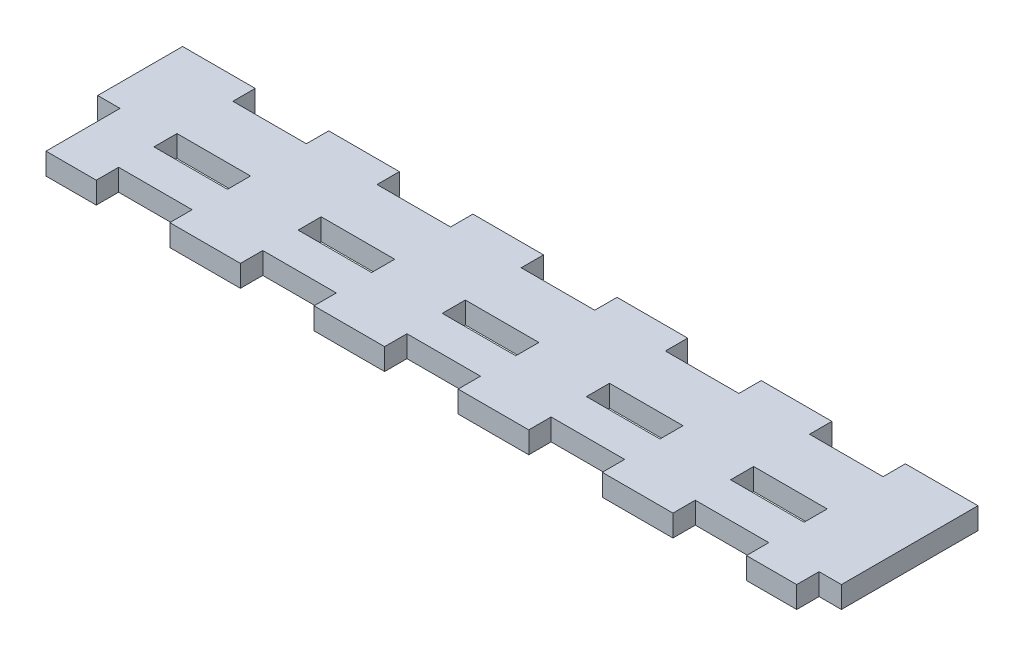
SolidWorks part; units mm, degrees
ref_plane "Front Plane" through (0, 0, 0) normal (0, 0, 1) x (1, 0, 0)
ref_plane "Top Plane" through (0, 0, 0) normal (0, 1, 0) x (1, 0, 0)
ref_plane "Right Plane" through (0, 0, 0) normal (1, 0, 0) x (0, 0, -1)
sketch "Sketch1" plane through (0, 0, 0) normal (0, 1, 0) x (1, 0, 0)
  line L0 (0, 0) -> (0, 21) construction
  line L2 (-55.1722, -44.793) -> (55.1722, -44.793)
  line L3 (-55.1722, -44.793) -> (-55.1722, -66.843)
  line L4 (-55.1722, -66.843) -> (55.1722, -66.843)
  line L5 (55.1722, -44.793) -> (55.1722, -66.843)
  circle A0 centre (0, 0) radius 21 construction
  circle A1 centre (0, 0) radius 21 construction
extrude "Boss-Extrude1" add sketch "Sketch1" against normal up to vertex (3 mm away)
sketch "Sketch2" plane through (0, 0, 0) normal (0, 1, 0) x (1, 0, 0)
  line L1 (-45, -55.743) -> (-35, -55.743)
  line L2 (45, -63.843) -> (45, -66.843)
  line L3 (-55.1722, -56.6708) -> (-52.1722, -56.6708) construction
  line L4 (55.1722, -44.793) -> (-55.1722, -44.793)
  line L5 (55.1722, -66.843) -> (55.1722, -44.793)
  line L6 (-55.1722, -66.843) -> (55.1722, -66.843)
  line L7 (-55.1722, -44.793) -> (-55.1722, -66.843)
  line L8 (55.1722, -44.793) -> (-55.1722, -44.793) construction
  line L9 (55.1722, -66.843) -> (55.1722, -44.793) construction
  line L10 (-55.1722, -66.843) -> (55.1722, -66.843) construction
  line L11 (-55.1722, -44.793) -> (-55.1722, -66.843) construction
  line L12 (-52.1722, -56.6708) -> (-52.1722, -66.843) construction
  line L14 (-45, -44.793) -> (-45, -47.793)
  line L15 (-45, -66.843) -> (-35, -66.843)
  line L16 (-35, -44.793) -> (-35, -47.793)
  line L17 (35, -63.843) -> (35, -66.843)
  line L18 (-25, -44.793) -> (-25, -47.793)
  line L19 (25, -63.843) -> (25, -66.843)
  line L20 (-15, -44.793) -> (-15, -47.793)
  line L21 (15, -63.843) -> (15, -66.843)
  line L22 (-5, -44.793) -> (-5, -47.793)
  line L23 (5, -63.843) -> (5, -66.843)
  line L24 (5, -44.793) -> (5, -47.793)
  line L25 (-5, -63.843) -> (-5, -66.843)
  line L26 (15, -44.793) -> (15, -47.793)
  line L27 (-15, -63.843) -> (-15, -66.843)
  line L28 (25, -44.793) -> (25, -47.793)
  line L29 (-25, -63.843) -> (-25, -66.843)
  line L30 (35, -44.793) -> (35, -47.793)
  line L31 (-35, -63.843) -> (-35, -66.843)
  line L32 (45, -44.793) -> (45, -47.793)
  line L33 (52.1722, -63.843) -> (55.1722, -63.843)
  line L34 (52.1722, -63.843) -> (52.1722, -66.843)
  line L37 (-45, -58.743) -> (-35, -58.743)
  line L38 (-45, -63.843) -> (-35, -63.843)
  line L39 (-45, -63.843) -> (-45, -66.843)
  line L40 (-45, -47.793) -> (-35, -47.793)
  line L41 (-45, -55.743) -> (-45, -58.743)
  line L42 (-35, -55.743) -> (-35, -58.743)
  line L43 (-25, -55.743) -> (-25, -58.743)
  line L44 (-15, -55.743) -> (-15, -58.743)
  line L45 (-5, -55.743) -> (-5, -58.743)
  line L46 (5, -55.743) -> (5, -58.743)
  line L47 (15, -55.743) -> (15, -58.743)
  line L48 (25, -55.743) -> (25, -58.743)
  line L49 (35, -55.743) -> (35, -58.743)
  line L50 (45, -55.743) -> (45, -58.743)
  line L51 (35, -47.793) -> (45, -47.793)
  line L52 (35, -55.743) -> (45, -55.743)
  line L53 (35, -58.743) -> (45, -58.743)
  line L54 (35, -63.843) -> (45, -63.843)
  line L55 (15, -63.843) -> (25, -63.843)
  line L56 (15, -58.743) -> (25, -58.743)
  line L57 (15, -55.743) -> (25, -55.743)
  line L58 (15, -47.793) -> (25, -47.793)
  line L59 (-5, -47.793) -> (5, -47.793)
  line L60 (-5, -55.743) -> (5, -55.743)
  line L61 (-5, -58.743) -> (5, -58.743)
  line L62 (-5, -63.843) -> (5, -63.843)
  line L63 (-25, -47.793) -> (-15, -47.793)
  line L64 (-25, -55.743) -> (-15, -55.743)
  line L65 (-25, -58.743) -> (-15, -58.743)
  line L66 (-25, -63.843) -> (-15, -63.843)
  dimension "D1" = 0
sketch "Sketch3" plane through (0, 0, 0) normal (0, 1, 0) x (1, 0, 0)
  line L0 (-45.1, -47.893) -> (-34.9, -47.893)
  line L1 (-55.2722, -56.5708) -> (-52.0722, -56.5708)
  line L2 (-55.2722, -56.5708) -> (-55.2722, -66.943)
  line L3 (-55.2722, -66.943) -> (-52.0722, -66.943)
  line L4 (-52.0722, -56.5708) -> (-52.0722, -66.943)
  line L5 (52.0722, -63.743) -> (55.2722, -63.743)
  line L6 (52.0722, -63.743) -> (52.0722, -66.943)
  line L7 (52.0722, -66.943) -> (55.2722, -66.943)
  line L8 (55.2722, -63.743) -> (55.2722, -66.943)
  line L9 (-45.1, -44.693) -> (-34.9, -44.693)
  line L10 (-45.1, -44.693) -> (-45.1, -47.893)
  line L11 (-45.1, -66.943) -> (-34.9, -66.943)
  line L12 (-34.9, -44.693) -> (-34.9, -47.893)
  line L13 (-25.1, -44.693) -> (-14.9, -44.693)
  line L14 (-25.1, -44.693) -> (-25.1, -47.893)
  line L15 (-25.1, -66.943) -> (-14.9, -66.943)
  line L16 (-14.9, -44.693) -> (-14.9, -47.893)
  line L17 (-5.1, -44.693) -> (5.1, -44.693)
  line L18 (-5.1, -44.693) -> (-5.1, -47.893)
  line L19 (-5.1, -66.943) -> (5.1, -66.943)
  line L20 (5.1, -44.693) -> (5.1, -47.893)
  line L21 (14.9, -44.693) -> (25.1, -44.693)
  line L22 (14.9, -44.693) -> (14.9, -47.893)
  line L23 (14.9, -66.943) -> (25.1, -66.943)
  line L24 (25.1, -44.693) -> (25.1, -47.893)
  line L25 (34.9, -44.693) -> (45.1, -44.693)
  line L26 (34.9, -44.693) -> (34.9, -47.893)
  line L27 (34.9, -66.943) -> (45.1, -66.943)
  line L28 (45.1, -44.693) -> (45.1, -47.893)
  line L29 (-45.1, -55.643) -> (-34.9, -55.643)
  line L30 (45.1, -58.843) -> (34.9, -58.843)
  line L31 (-45.1, -63.743) -> (-34.9, -63.743)
  line L32 (-45.1, -55.643) -> (-45.1, -58.843)
  line L33 (-34.9, -55.643) -> (-34.9, -58.843)
  line L34 (-25.1, -47.893) -> (-14.9, -47.893)
  line L35 (-25.1, -55.643) -> (-14.9, -55.643)
  line L36 (-34.9, -58.843) -> (-45.1, -58.843)
  line L37 (-25.1, -63.743) -> (-14.9, -63.743)
  line L38 (-34.9, -63.743) -> (-34.9, -66.943)
  line L39 (-45.1, -63.743) -> (-45.1, -66.943)
  line L40 (-25.1, -63.743) -> (-25.1, -66.943)
  line L41 (-14.9, -63.743) -> (-14.9, -66.943)
  line L42 (-5.1, -63.743) -> (-5.1, -66.943)
  line L43 (5.1, -63.743) -> (5.1, -66.943)
  line L44 (14.9, -63.743) -> (14.9, -66.943)
  line L45 (25.1, -63.743) -> (25.1, -66.943)
  line L46 (34.9, -63.743) -> (34.9, -66.943)
  line L47 (45.1, -63.743) -> (45.1, -66.943)
  line L48 (25.1, -58.843) -> (14.9, -58.843)
  line L49 (34.9, -63.743) -> (45.1, -63.743)
  line L50 (14.9, -63.743) -> (25.1, -63.743)
  line L51 (5.1, -58.843) -> (-5.1, -58.843)
  line L52 (-14.9, -58.843) -> (-25.1, -58.843)
  line L53 (-5.1, -63.743) -> (5.1, -63.743)
  line L54 (-5.1, -55.643) -> (5.1, -55.643)
  line L55 (-14.9, -55.643) -> (-14.9, -58.843)
  line L56 (-5.1, -47.893) -> (5.1, -47.893)
  line L57 (-25.1, -55.643) -> (-25.1, -58.843)
  line L58 (-5.1, -55.643) -> (-5.1, -58.843)
  line L59 (5.1, -55.643) -> (5.1, -58.843)
  line L60 (14.9, -47.893) -> (25.1, -47.893)
  line L61 (14.9, -55.643) -> (25.1, -55.643)
  line L62 (14.9, -55.643) -> (14.9, -58.843)
  line L63 (25.1, -55.643) -> (25.1, -58.843)
  line L64 (34.9, -55.643) -> (45.1, -55.643)
  line L65 (34.9, -47.893) -> (45.1, -47.893)
  line L66 (34.9, -55.643) -> (34.9, -58.843)
  line L67 (45.1, -55.643) -> (45.1, -58.843)
  line L68 (-45, -47.793) -> (-44.9, -47.793) construction
  line L69 (-44.9, -47.793) -> (-44.9, -47.893) construction
  line L70 (-45, -47.793) -> (-45.1, -47.793) construction
  line L72 (-35, -44.793) -> (-34.9, -44.793) construction
  line L73 (-35, -44.793) -> (-35, -44.693) construction
  line L74 (-45, -55.743) -> (-45, -55.643) construction
  line L75 (-45, -58.743) -> (-45, -58.843) construction
  line L76 (-45, -63.843) -> (-45, -63.743) construction
  line L77 (-45, -66.843) -> (-45, -66.943) construction
  line L78 (-25, -44.793) -> (-25.1, -44.793) construction
  line L79 (-15, -44.793) -> (-14.9, -44.793) construction
  line L80 (5, -44.793) -> (5.1, -44.793) construction
  line L81 (-5, -44.793) -> (-5.1, -44.793) construction
  line L82 (55.1722, -63.843) -> (55.2722, -63.843) construction
  line L83 (52.1722, -63.843) -> (52.0722, -63.843) construction
  line L84 (35, -44.793) -> (34.9, -44.793) construction
  line L85 (45, -44.793) -> (45.1, -44.793) construction
  line L86 (15, -44.793) -> (14.9, -44.793) construction
  line L87 (25, -44.793) -> (25.1, -44.793) construction
  line L88 (-52.1722, -56.6708) -> (-52.1722, -56.5708) construction
  line L89 (-52.1722, -56.6708) -> (-52.0722, -56.6708) construction
  line L90 (-55.1722, -56.6708) -> (-55.2722, -56.6708) construction
extrude "Cut-Extrude1" cut sketch "Sketch3" against normal through all
